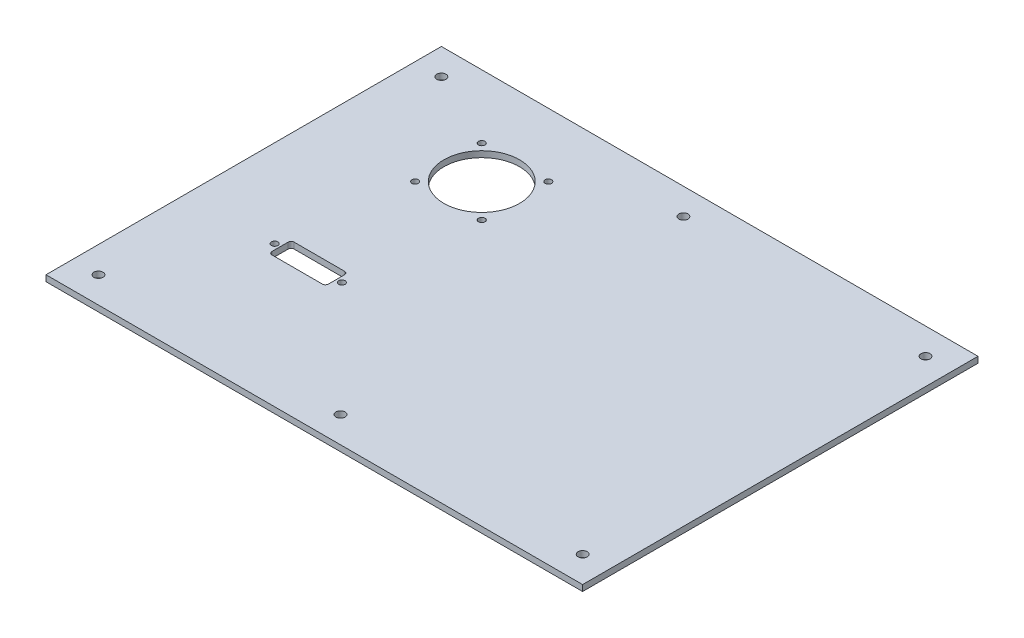
SolidWorks part; units mm, degrees
ref_plane "Спереди" through (0, 0, 0) normal (0, 0, 1) x (1, 0, 0)
ref_plane "Сверху" through (0, 0, 0) normal (0, 1, 0) x (1, 0, 0)
ref_plane "Справа" through (0, 0, 0) normal (1, 0, 0) x (0, 0, -1)
sketch "Эскиз1" plane through (0, 0, 0) normal (0, 1, 0) x (1, 0, 0)
  line L0 (0, 0) -> (266, 0)
  line L1 (0, 0) -> (0, 196)
  line L2 (266, 0) -> (266, 196)
  line L3 (0, 196) -> (266, 196)
  line L4 (13, 183) -> (253, 183) construction
  line L5 (13, 183) -> (13, 13) construction
  line L6 (253, 183) -> (253, 13) construction
  line L7 (13, 13) -> (253, 13) construction
  circle A0 centre (13, 183) radius 2.25
  circle A1 centre (253, 183) radius 2.25
  circle A2 centre (253, 13) radius 2.25
  circle A3 centre (13, 13) radius 2.25
  circle A4 centre (133, 13) radius 2.25
  circle A5 centre (133, 183) radius 2.25
  dimension "D7" = 4.5
  dimension "D8" = 4.5
  dimension "D9" = 4.5
  dimension "D10" = 4.5
  dimension "D11" = 4.5
  dimension "D12" = 4.5
  dimension "D1" = 196
  dimension "D2" = 266
  dimension "D3" = 13
  dimension "D4" = 13
  dimension "D5" = 13
  dimension "D6" = 13
extrude "Бобышка-Вытянуть1" add sketch "Эскиз1" along normal blind 3
sketch "Эскиз2" plane through (0, 3, 0) normal (0, 1, 0) x (1, 0, 0)
  line L0 (3, 193) -> (3, 3) construction
  line L1 (3, 193) -> (263, 193) construction
  line L2 (3, 3) -> (263, 3) construction
  line L3 (263, 193) -> (263, 3) construction
  line L4 (0, 0) -> (266, 0) construction
  line L5 (0, 196) -> (0, 0) construction
  dimension "D1" = 190
  dimension "D2" = 260
  dimension "D3" = 3
  dimension "D4" = 3
sketch "Эскиз3" plane through (0, 3, 0) normal (0, 1, 0) x (1, 0, 0)
  circle A0 centre (68, 148) radius 18.75 construction
  circle A1 centre (68, 148) radius 18.75
  circle A2 centre (84.5, 164.5) radius 1.6 construction
  circle A3 centre (84.5, 164.5) radius 1.6
  circle A4 centre (84.5, 131.5) radius 1.6 construction
  circle A5 centre (84.5, 131.5) radius 1.6
  circle A6 centre (51.5, 131.5) radius 1.6 construction
  circle A7 centre (51.5, 131.5) radius 1.6
  circle A8 centre (51.5, 164.5) radius 1.6 construction
  circle A9 centre (51.5, 164.5) radius 1.6
extrude "Вырез-Вытянуть1" cut sketch "Эскиз3" against normal through all
sketch "Sketch1" plane through (0, 3, 0) normal (0, 1, 0) x (1, 0, 0)
  line L0 (0, 70) -> (107.5357, 70) construction
  line L1 (0, 196) -> (0, 0) construction
  line L2 (46, 75.5) -> (46, 64.5)
  line L3 (46, 75.5) -> (74, 75.5)
  line L4 (46, 64.5) -> (74, 64.5)
  line L5 (74, 75.5) -> (74, 64.5)
  line L6 (60, 75.5) -> (60, 64.5) construction
  line L7 (46, 70) -> (74, 70) construction
  line L8 (0, 0) -> (266, 0) construction
  line L9 (43.34, 71.6) -> (76.66, 71.6) construction
  line L10 (43.34, 68.4) -> (76.66, 68.4) construction
  line L11 (60, 71.6) -> (60, 68.4) construction
  circle A0 centre (43.34, 70) radius 1.6
  circle A1 centre (76.66, 70) radius 1.6
  dimension "D5" = 33.32
  dimension "D6" = 3.2
  dimension "D1" = 28
  dimension "D2" = 11
  dimension "D3" = 70
  dimension "D4" = 60
extrude "Cut-Extrude1" cut sketch "Sketch1" against normal through all
fillet "Fillet1" radius 1.5 4 edges at (74, 1.5, -64.5) (74, 1.5, -75.5) (46, 1.5, -64.5) (46, 1.5, -75.5)
